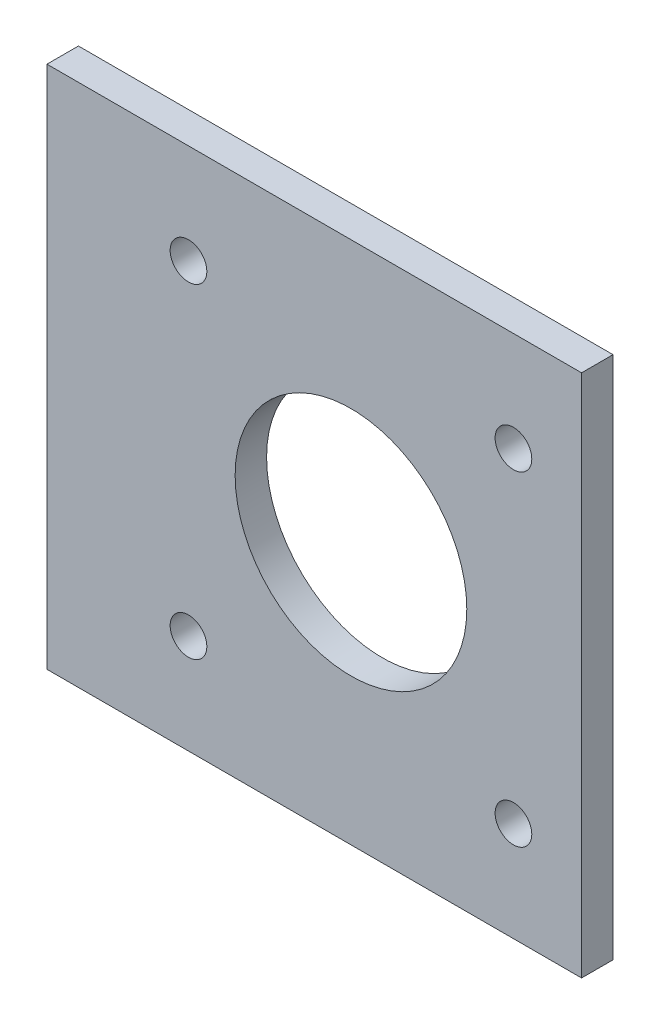
SolidWorks part; units mm, degrees
material "Haya"
ref_plane "Alzado" through (0, 0, 0) normal (0, 0, 1) x (1, 0, 0)
ref_plane "Planta" through (0, 0, 0) normal (0, 1, 0) x (1, 0, 0)
ref_plane "Vista lateral" through (0, 0, 0) normal (1, 0, 0) x (0, 0, -1)
sketch "Croquis1" plane through (0, 0, 0) normal (0, 0, 1) x (1, 0, 0)
  line L0 (51, -5) -> (51, -45) construction
  line L1 (0, 0) -> (51, 0)
  line L2 (0, 0) -> (0, -50)
  line L3 (0, -50) -> (51, -50)
  line L4 (51, 0) -> (51, -50)
  line L5 (46, -50) -> (5, -50) construction
  circle A0 centre (29, -25) radius 11.05
  circle A1 centre (29, -25) radius 11.05 construction
  circle A2 centre (44.5, -40.5) radius 1.75
  circle A3 centre (13.5, -40.5) radius 1.75
  circle A4 centre (13.5, -9.5) radius 1.75
  circle A5 centre (44.5, -9.5) radius 1.75
  dimension "D1" = 3.5
  dimension "D2" = 2
  dimension "D3" = 2
extrude "Saliente-Extruir1" add sketch "Croquis1" along normal blind 3
